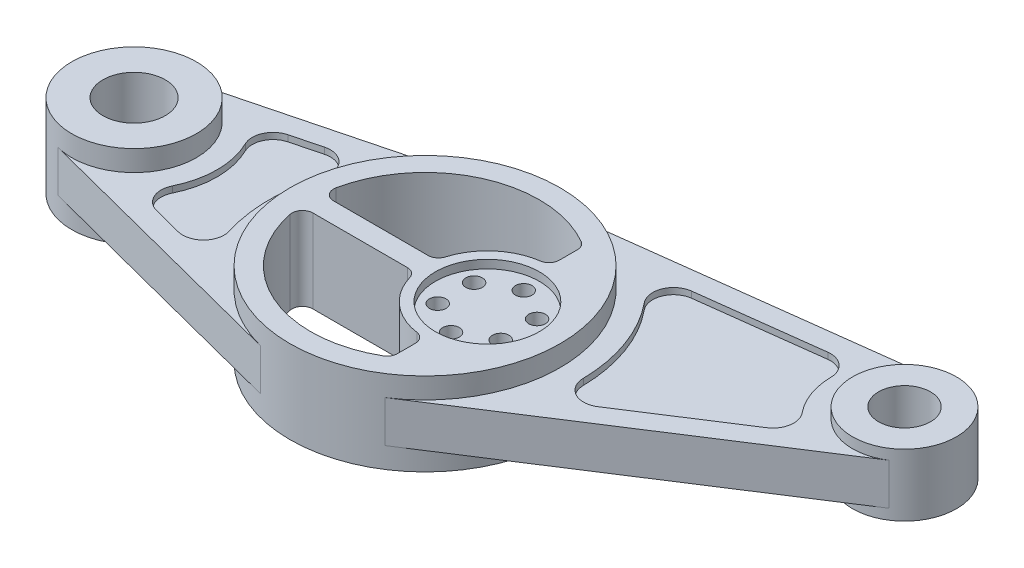
SolidWorks part; units mm, degrees
material "AISI 1020"
ref_plane "Front Plane" through (0, 0, 0) normal (0, 0, 1) x (1, 0, 0)
ref_plane "Top Plane" through (0, 0, 0) normal (0, 1, 0) x (1, 0, 0)
ref_plane "Right Plane" through (0, 0, 0) normal (1, 0, 0) x (0, 0, -1)
sketch "Sketch1" plane through (0, 0, 0) normal (0, 1, 0) x (1, 0, 0)
  line L0 (-140, 0) -> (0, 0) construction
  line L1 (0, 0) -> (169.1447, 61.5636) construction
  line L2 (-147.5, 29.0474) -> (-16.25, 62.936)
  line L3 (-147.5, -29.0474) -> (-16.25, -62.936)
  line L4 (-8.1021, 64.4931) -> (166.0285, 86.3687)
  line L7 (35.2488, -54.6125) -> (182.7019, 40.5588)
  arc A0 (-16.25, -62.936) -> (35.2488, -54.6125) centre (0, 0) ccw
  arc A1 (-147.5, 29.0474) -> (-147.5, -29.0474) centre (-140, 0) ccw
  arc A2 (182.7019, 40.5588) -> (166.0285, 86.3687) centre (169.1447, 61.5636) ccw
  arc A3 (-8.1021, 64.4931) -> (-16.25, 62.936) centre (0, 0) ccw
  dimension "D1" = 65
  dimension "D2" = 25
  dimension "D3" = 30
  dimension "D4" = 140
  dimension "D5" = 20
  dimension "D6" = 180
extrude "Boss-Extrude1" add sketch "Sketch1" along normal mid plane 20
sketch "Sketch2" plane through (0, 0, 0) normal (0, 1, 0) x (1, 0, 0)
  circle A0 centre (0, 0) radius 65
  arc A1 (-16.25, -62.936) -> (35.2488, -54.6125) centre (0, 0) ccw construction
extrude "Boss-Extrude2" add sketch "Sketch2" along normal mid plane 40
sketch "Sketch3" plane through (0, 0, 0) normal (0, 1, 0) x (1, 0, 0)
  circle A0 centre (-140, 0) radius 30
  arc A1 (-147.5, 29.0474) -> (-147.5, -29.0474) centre (-140, 0) ccw construction
extrude "Boss-Extrude3" add sketch "Sketch3" along normal mid plane 40
sketch "Sketch5" plane through (0, 0, 0) normal (0, 1, 0) x (1, 0, 0)
  circle A0 centre (169.1447, 61.5636) radius 25
  arc A1 (182.7019, 40.5588) -> (166.0285, 86.3687) centre (169.1447, 61.5636) ccw construction
extrude "Boss-Extrude4" add sketch "Sketch5" along normal mid plane 30
sketch "Sketch6" plane through (0, 20, 0) normal (0, 1, 0) x (1, 0, 0)
  line L0 (0, 0) -> (-93.4594, 0) construction
  line L1 (-48.9898, 5) -> (-3.541, 5)
  line L3 (30, 34.641) -> (30, 43.3013)
  arc A0 (27.5, 47.6314) -> (-53.8888, 11) centre (0, 0) ccw
  arc A1 (25.7143, 29.6923) -> (1.2506, 8.5714) centre (30, 0) ccw
  arc A2 (-48.9898, 5) -> (-53.8888, 11) centre (-48.9898, 10) cw
  arc A3 (-3.541, 5) -> (1.2506, 8.5714) centre (-3.541, 10) ccw
  arc A4 (30, 34.641) -> (25.7143, 29.6923) centre (25, 34.641) cw
  arc A5 (30, 43.3013) -> (27.5, 47.6314) centre (25, 43.3013) ccw
  dimension "D1" = 55
  dimension "D4" = 30
  dimension "D6" = 5
  dimension "D2" = 5
  dimension "D3" = 30
extrude "Cut-Extrude1" cut sketch "Sketch6" against normal through all
mirror "Mirror1" about plane through (0, 0, 0) normal (0, 0, 1) of "Cut-Extrude1"
sketch "Sketch8" plane through (0, 20, 0) normal (0, 1, 0) x (1, 0, 0)
  circle A0 centre (30, 0) radius 25
  dimension "D1" = 50
extrude "Cut-Extrude3" cut sketch "Sketch8" against normal blind 4
mirror "Mirror2" about plane through (0, 0, 0) normal (0, 1, 0) of "Cut-Extrude3"
sketch "Sketch9" plane through (0, 16, 0) normal (0, 1, 0) x (1, 0, 0)
  circle A0 centre (30, 17.5) radius 4
  circle A1 centre (30, 0) radius 17.5 construction
  dimension "D1" = 8
  dimension "D2" = 35
extrude "Cut-Extrude4" cut sketch "Sketch9" against normal through all
pattern_circular "CirPattern1" count 6 over 360 about axis through (30, 0, 0) along (0, 1, 0) of "Cut-Extrude4"
sketch "Sketch10" plane through (0, 20, 0) normal (0, 1, 0) x (1, 0, 0)
  circle A0 centre (-140, 0) radius 15
  dimension "D1" = 30
extrude "Cut-Extrude5" cut sketch "Sketch10" against normal through all
sketch "Sketch11" plane through (0, 15, 0) normal (0, 1, 0) x (1, 0, 0)
  circle A0 centre (169.1447, 61.5636) radius 12.5
  dimension "D1" = 25
extrude "Cut-Extrude6" cut sketch "Sketch11" against normal through all
sketch "Sketch12" plane through (0, 10, 0) normal (0, 1, 0) x (1, 0, 0)
  line L40 (72.6674, -18.5592) -> (150.7098, 31.8121)
  line L41 (135.8988, 72.5049) -> (43.7369, 60.9269)
  line L42 (72.6674, -18.5592) -> (150.7098, 31.8121)
  line L43 (135.8988, 72.5049) -> (43.7369, 60.9269)
  line L46 (-63.121, 40.506) -> (-111.459, 28.0252)
  line L47 (-111.459, -28.0252) -> (-63.121, -40.506)
  line L48 (-63.121, 40.506) -> (-111.459, 28.0252)
  line L49 (-111.459, -28.0252) -> (-63.121, -40.506)
  arc A48 (135.8988, 72.5049) -> (150.7098, 31.8121) centre (169.1447, 61.5636) ccw
  arc A49 (72.6674, -18.5592) -> (43.7369, 60.9269) centre (0, 0) ccw
  arc A50 (135.8988, 72.5049) -> (150.7098, 31.8121) centre (169.1447, 61.5636) ccw
  arc A51 (72.6674, -18.5592) -> (43.7369, 60.9269) centre (0, 0) ccw
  arc A54 (-111.459, -28.0252) -> (-111.459, 28.0252) centre (-140, 0) ccw
  arc A55 (-63.121, 40.506) -> (-63.121, -40.506) centre (0, 0) ccw
  arc A56 (-111.459, -28.0252) -> (-111.459, 28.0252) centre (-140, 0) ccw
  arc A57 (-63.121, 40.506) -> (-63.121, -40.506) centre (0, 0) ccw
  dimension "D1" = 10
  dimension "D2" = 10
extrude "Cut-Extrude7" cut sketch "Sketch12" against normal blind 3
fillet "Fillet1" radius 10 8 edges at (72.6674, 8.5, 18.5592) (150.7098, 8.5, -31.8121) (135.8988, 8.5, -72.5049) (43.7369, 8.5, -60.9269) (-63.121, 8.5, 40.506) (-111.459, 8.5, 28.0252) (-63.121, 8.5, -40.506) (-111.459, 8.5, -28.0252)
mirror "Mirror3" about plane through (0, 0, 0) normal (0, 1, 0) of "Cut-Extrude7", "Fillet1"
